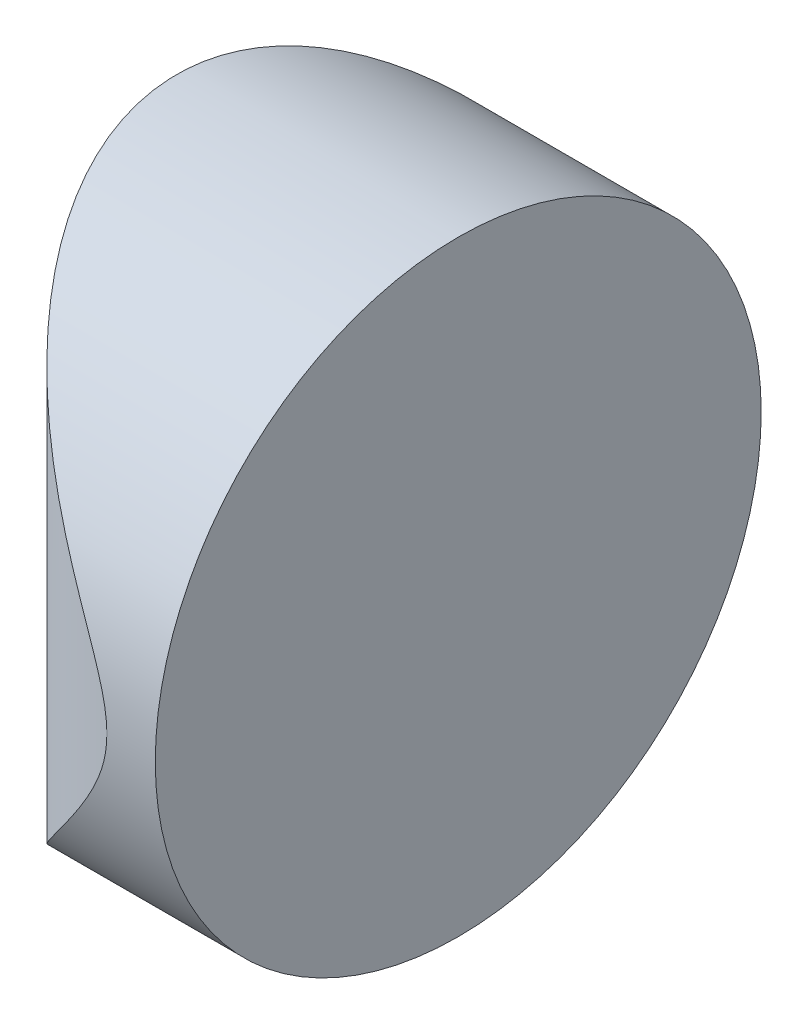
SolidWorks part; units mm, degrees
ref_plane "前视基准面" through (0, 0, 0) normal (0, 0, 1) x (1, 0, 0)
ref_plane "上视基准面" through (0, 0, 0) normal (0, 1, 0) x (1, 0, 0)
ref_plane "右视基准面" through (0, 0, 0) normal (1, 0, 0) x (0, 0, -1)
sketch "草图1" plane through (0, 0, 0) normal (0, 1, 0) x (1, 0, 0)
  line L0 (10.7432, 0) -> (-55.502, 0) construction
  line L1 (1.0484, 12.5) -> (3.0452, 12.5)
  line L2 (1.0484, -12.5) -> (3.0452, -12.5)
  line L3 (3.0452, 12.5) -> (3.0452, -12.5)
  arc A0 (1.0484, 12.5) -> (1.0484, -12.5) centre (4.3552, 0) ccw
  point P19 (-8.5748, 0)
  point P20 (3.0452, 0)
  dimension "D2" = 12.5
  dimension "D3" = 12.93
  dimension "D4" = 11.62
  dimension "D1" = 12.5
extrude "凸台-拉伸1" add sketch "草图1" along normal blind 25 contours A0 L2 L3 L1
sketch "草图2" plane through (3.0452, 0, 0) normal (1, 0, 0) x (0, 0, -1)
  line L0 (12.5, 0) -> (-12.5, 0) construction
  line L7 (-12.5, 0) -> (12.5, 0)
  line L8 (12.5, 0) -> (12.5, 25)
  line L9 (12.5, 25) -> (-12.5, 25)
  line L10 (-12.5, 25) -> (-12.5, 0)
  line L11 (-12.5, 0) -> (12.5, 0)
  line L12 (12.5, 0) -> (12.5, 25)
  line L13 (12.5, 25) -> (-12.5, 25)
  line L14 (-12.5, 25) -> (-12.5, 0)
  circle A0 centre (0, 12.5) radius 12.5
  point P2 (0, 0)
  line M1 (-12.5, 0) -> (12.5, 0)
  line M2 (12.5, 0) -> (12.5, 25)
  line M3 (12.5, 25) -> (-12.5, 25)
  line M4 (-12.5, 25) -> (-12.5, 0)
  dimension "D1" = 25
  dimension "D4" = 12.5
  dimension "D2" = 12.5
  dimension "D3" = 0
extrude "切除-拉伸8" cut sketch "草图2" against normal blind 12.7 contours A0 L13 M4 | A0 L12 M3 | A0 L11 M2 | A0 L14 M1
